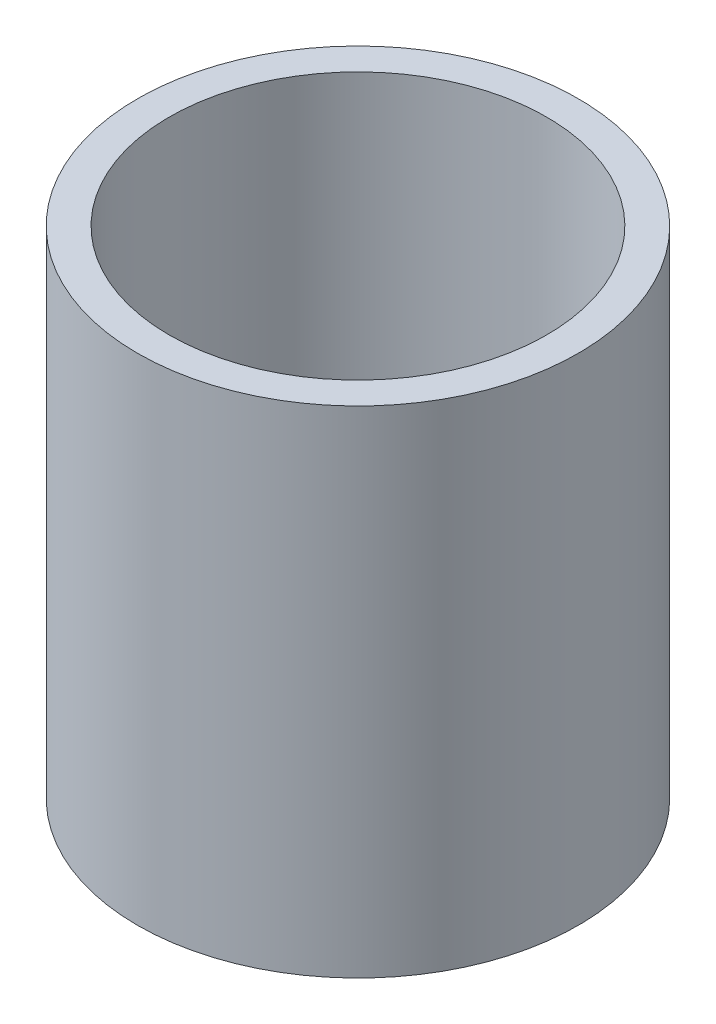
SolidWorks part; units mm, degrees
ref_plane "Front Plane" through (0, 0, 0) normal (0, 0, 1) x (1, 0, 0)
ref_plane "Top Plane" through (0, 0, 0) normal (0, 1, 0) x (1, 0, 0)
ref_plane "Right Plane" through (0, 0, 0) normal (1, 0, 0) x (0, 0, -1)
sketch "Sketch1" plane through (0, 0, 0) normal (0, 1, 0) x (1, 0, 0)
  circle A0 centre (0, 0) radius 38.1
  circle A1 centre (0, 0) radius 41.6
  circle A2 centre (0, 0) radius 44.5
  dimension "D1" = 3.5
  dimension "D2" = 76.2
extrude "Boss-Extrude1" add sketch "Sketch1" against normal blind 100 contours A2 A1 | A1 A0
